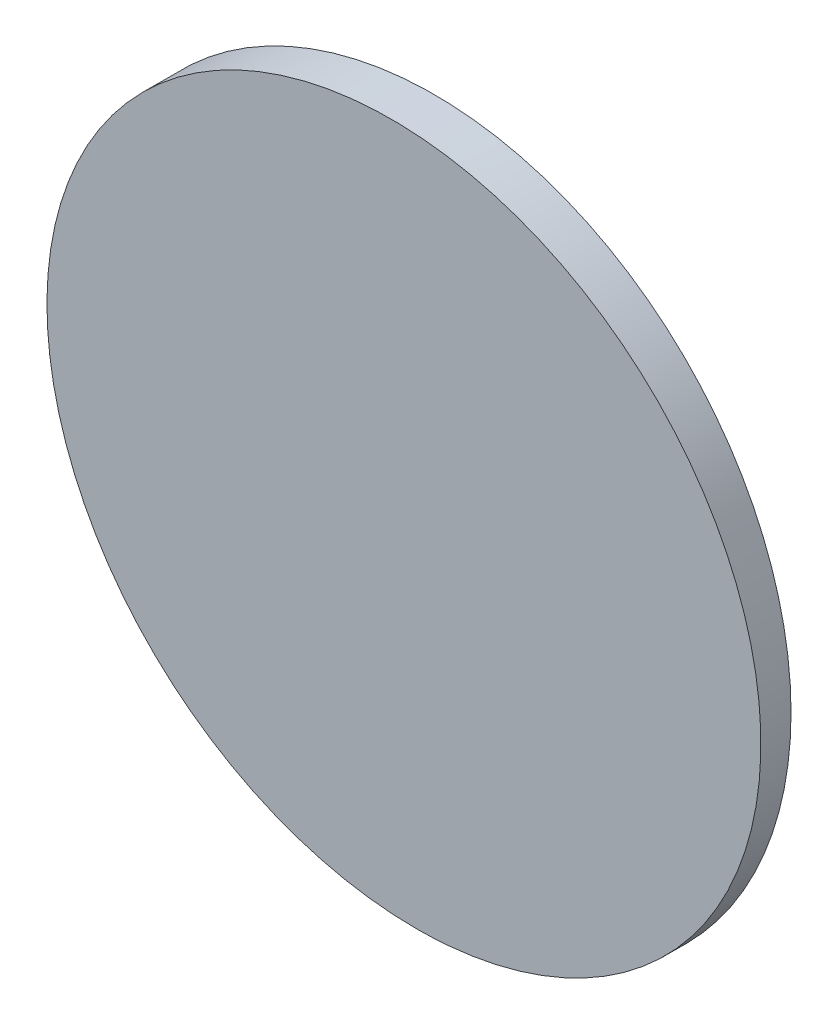
SolidWorks part; units mm, degrees
ref_plane "前视基准面" through (0, 0, 0) normal (0, 0, 1) x (1, 0, 0)
ref_plane "上视基准面" through (0, 0, 0) normal (0, 1, 0) x (1, 0, 0)
ref_plane "右视基准面" through (0, 0, 0) normal (1, 0, 0) x (0, 0, -1)
sketch "草图2" plane through (0, 0, 0) normal (0, 0, 1) x (1, 0, 0)
  circle A0 centre (0, 0) radius 50
  dimension "D1" = 100
extrude "凸台-拉伸1" add sketch "草图2" along normal blind 6
sketch "草图3" plane through (0, 0, 0) normal (1, 0, 0) x (0, 0, -1)
  line L4 (-6, -50) -> (-6, 50)
  line L6 (-6, 50) -> (-6, -50) construction
  line L8 (-6, 50) -> (-2.5079, -50)
  line L9 (-6, -50) -> (-2.5079, -50)
  dimension "D1" = 100
  dimension "D3" = 2
  dimension "D4" = 3.4921
extrude "切除-拉伸1" cut sketch "草图3" against normal mid plane 100
